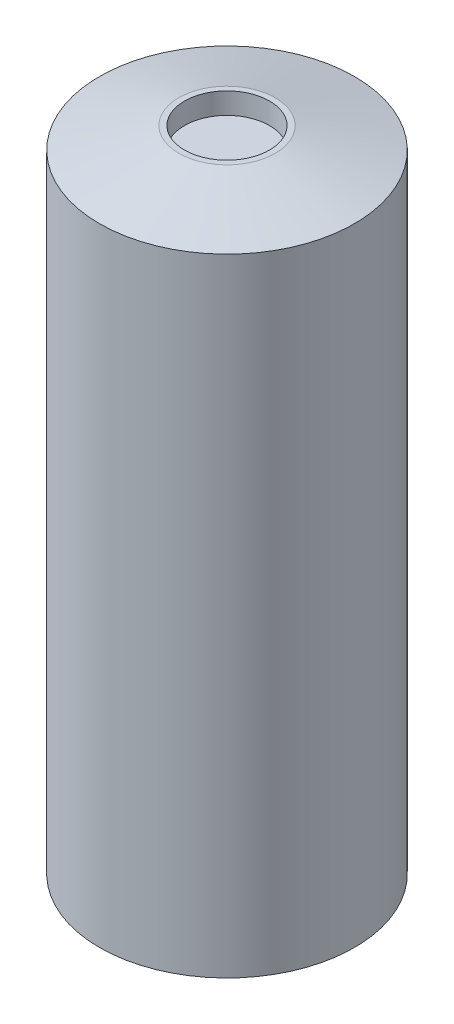
SolidWorks part; units mm, degrees
ref_plane "Plan de face" through (0, 0, 0) normal (0, 0, 1) x (1, 0, 0)
ref_plane "Plan de dessus" through (0, 0, 0) normal (0, 1, 0) x (1, 0, 0)
ref_plane "Plan de droite" through (0, 0, 0) normal (1, 0, 0) x (0, 0, -1)
sketch "Esquisse1" plane through (0, 0, 0) normal (0, 1, 0) x (1, 0, 0)
  circle A0 centre (0, 0) radius 6
  dimension "D1" = 12
extrude "Extrusion1" add sketch "Esquisse1" along normal blind 30.5
chamfer "Chanfrein1" distance 1 angle 75 1 edges at (0, 30.5, 6)
sketch "Esquisse2" plane through (0, 30.5, 0) normal (0, 1, 0) x (1, 0, 0)
  circle A0 centre (0, 0) radius 2
  dimension "D1" = 4
extrude "Enlèv. mat.-Extru.1" cut sketch "Esquisse2" against normal blind 1
